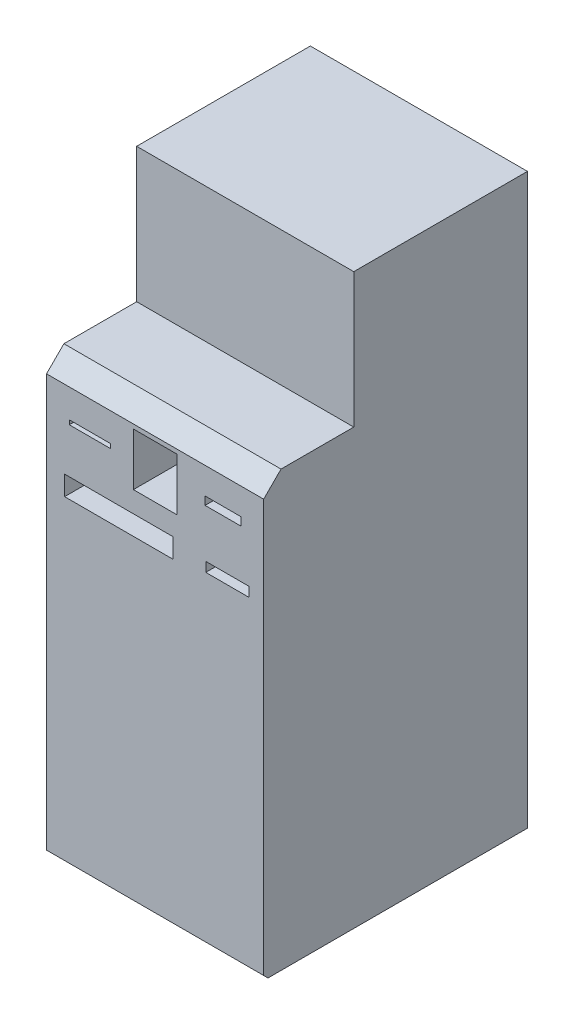
SolidWorks part; units mm, degrees
ref_plane "Front Plane" through (0, 0, 0) normal (0, 0, 1) x (1, 0, 0)
ref_plane "Top Plane" through (0, 0, 0) normal (0, 1, 0) x (1, 0, 0)
ref_plane "Right Plane" through (0, 0, 0) normal (1, 0, 0) x (0, 0, -1)
sketch "Sketch1" plane through (0, 0, 0) normal (1, 0, 0) x (0, 0, -1)
  line L0 (0, 0) -> (-190, 0)
  line L1 (-200, 10) -> (-200, 960)
  line L2 (-160, 1000) -> (7.5261, 1000)
  line L3 (7.5261, 1000) -> (7.5261, 1310)
  line L4 (407.5261, 970) -> (407.5261, 820)
  line L6 (7.5261, 1310) -> (57.5261, 1310)
  line L7 (57.5261, 1310) -> (385.0684, 1019.8911) construction
  line L8 (-160, 1000) -> (-200, 960)
  line L9 (407.5261, 820) -> (407.5261, 0)
  line L10 (407.5261, 0) -> (0, 0)
  line L14 (-190, 0) -> (-200, 10)
  line L19 (407.5261, 1000) -> (407.5261, 1310)
  line L20 (407.5261, 1310) -> (57.5261, 1310)
  line L21 (385.0684, 1019.8911) -> (407.5261, 970) construction
  line L24 (407.5261, 1000) -> (407.5261, 970)
  arc A0 (407.5261, 1000) -> (7.5261, 1310) centre (87.4011, 1000) ccw construction
  arc A1 (-200, 960) -> (-160, 1000) centre (-160, 960) cw construction
  point P1 (-200, 0)
  dimension "D5" = 40
  dimension "D2" = 200
  dimension "D3" = 310
  dimension "D6" = 50
  dimension "D7" = 400
extrude "Boss-Extrude1" add sketch "Sketch1" along normal blind 500
sketch "Sketch2" plane through (0, 0, 200) normal (0, 0, 1) x (1, 0, 0)
  line L0 (366.6667, 758.294) -> (291.6667, 758.294) construction
  line L1 (200, 950) -> (300, 950)
  line L2 (200, 950) -> (200, 829)
  line L3 (200, 829) -> (300, 829)
  line L4 (300, 950) -> (300, 829)
  line L5 (300, 889.5) -> (365.11, 889.5) construction
  line L6 (365.11, 889.5) -> (447.65, 889.5) construction
  line L7 (147.65, 894.5) -> (52.35, 894.5)
  line L8 (147.65, 894.5) -> (147.65, 884.5)
  line L9 (147.65, 884.5) -> (52.35, 884.5)
  line L10 (52.35, 894.5) -> (52.35, 884.5)
  line L11 (300, 950) -> (500, 950) construction
  line L12 (500, 960) -> (500, 10) construction
  line L13 (147.65, 889.5) -> (200, 889.5) construction
  line L14 (365.11, 898.9) -> (447.65, 898.9)
  line L15 (365.11, 898.9) -> (365.11, 880.1)
  line L16 (365.11, 880.1) -> (447.65, 880.1)
  line L17 (447.65, 898.9) -> (447.65, 880.1)
  line L18 (250, 950) -> (250, 960) construction
  line L19 (147.65, 894.5) -> (500, 894.5) construction
  line L20 (500, 960) -> (500, 10) construction
  line L21 (500, 960) -> (0, 960) construction
  line L22 (52.35, 894.5) -> (0, 894.5) construction
  line L23 (0, 960) -> (0, 10) construction
  line L24 (365.11, 898.9) -> (312.7601, 898.8175) construction
  line L25 (366.6667, 747.294) -> (466.6667, 747.294)
  line L26 (366.6667, 747.294) -> (366.6667, 769.294)
  line L27 (366.6667, 769.294) -> (466.6667, 769.294)
  line L28 (466.6667, 747.294) -> (466.6667, 769.294)
  line L29 (447.65, 898.9) -> (500, 898.9) construction
  line L30 (41.6667, 780.794) -> (291.6667, 780.794)
  line L31 (41.6667, 780.794) -> (41.6667, 735.794)
  line L32 (41.6667, 735.794) -> (291.6667, 735.794)
  line L33 (291.6667, 780.794) -> (291.6667, 735.794)
  line L34 (500, 714.5982) -> (333.3333, 714.5982) construction
  line L35 (333.3333, 714.5982) -> (0, 714.5982) construction
  line L36 (416.6667, 714.5982) -> (416.6667, 747.294) construction
  line L37 (166.6667, 714.5982) -> (166.6667, 735.794) construction
  dimension "D1" = 121
  dimension "D2" = 100
  dimension "D3" = 10
  dimension "D4" = 166.6667
  dimension "D5" = 95.3
  dimension "D6" = 10
  dimension "D7" = 82.54
  dimension "D8" = 18.8
  dimension "D10" = 22
  dimension "D11" = 100
  dimension "D12" = 250
  dimension "D13" = 45
extrude "Cut-Extrude1" cut sketch "Sketch2" against normal blind 268
